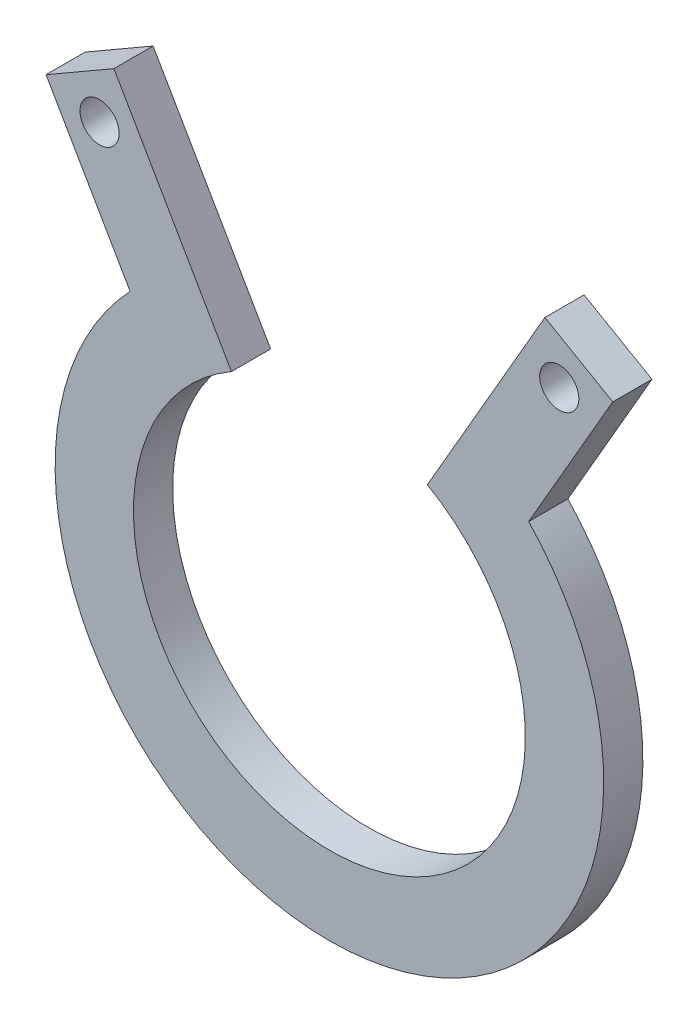
SolidWorks part; units mm, degrees
ref_plane "Front Plane" through (0, 0, 0) normal (0, 0, 1) x (1, 0, 0)
ref_plane "Top Plane" through (0, 0, 0) normal (0, 1, 0) x (1, 0, 0)
ref_plane "Right Plane" through (0, 0, 0) normal (1, 0, 0) x (0, 0, -1)
sketch "Sketch2" plane through (0, 0, 0) normal (0, 0, 1) x (1, 0, 0)
  circle A0 centre (0, 0) radius 19.05
  circle A1 centre (0, 0) radius 22.225
  circle A2 centre (0, 0) radius 15.875
  dimension "D1" = 38.1
  dimension "D2" = 3.175
  dimension "D3" = 3.175
extrude "Boss-Extrude1" add sketch "Sketch2" along normal blind 3.175 contours A1 A0 | A0 A2
sketch "Sketch3" plane through (0, 0, 3.175) normal (0, 0, 1) x (1, 0, 0)
  line L0 (-20.2121, 28.6584) -> (-18.6246, 25.9088) construction
  line L1 (0, 0) -> (-11.1125, 19.2474) construction
  line L2 (0, 0) -> (0, 22.225) construction
  line L3 (-11.1125, 19.2474) -> (-17.4625, 30.2459)
  line L4 (-17.4625, 30.2459) -> (-22.9618, 27.0709)
  line L5 (-22.9618, 27.0709) -> (-16.1485, 15.2701)
  line L6 (-17.4625, 30.2459) -> (-10.6493, 18.4451)
  line L7 (-16.6118, 16.0724) -> (-22.9618, 27.0709)
  line L8 (20.2121, 28.6584) -> (18.6246, 25.9088) construction
  line L9 (16.6118, 16.0724) -> (22.9618, 27.0709)
  line L10 (17.4625, 30.2459) -> (10.6493, 18.4451)
  line L11 (22.9618, 27.0709) -> (16.1485, 15.2701)
  line L12 (17.4625, 30.2459) -> (22.9618, 27.0709)
  line L13 (11.1125, 19.2474) -> (17.4625, 30.2459)
  circle A0 centre (0, 0) radius 22.225 construction
  circle A2 centre (-18.6246, 25.9088) radius 1.5875
  circle A3 centre (18.6246, 25.9088) radius 1.5875
  circle M7 centre (0, 0) radius 22.225
  dimension "D5" = 3.175
  dimension "D1" = 30
  dimension "D2" = 3.175
  dimension "D3" = 12.7
  dimension "D4" = 6.35
extrude "Boss-Extrude2" add sketch "Sketch3" against normal up to surface (3.175 mm away) contours L4 L5 L3 A2 M7 | L12 L10 L11 L9 A3 M7 up to face at (22.225, 0, 0)
ref_plane "Plane4" through (-17.4625, 30.2459, 3.175) normal (0, 0, 1) x (1, 0, 0)
sketch "Sketch5" plane through (0, 0, 3.175) normal (0, 0, 1) x (1, 0, 0)
  line L0 (-11.1125, 19.2474) -> (0, 0)
  line L1 (0, 0) -> (11.1125, 19.2474)
  arc A0 (11.1125, 19.2474) -> (-11.1125, 19.2474) centre (0, 0) ccw construction
  arc A1 (11.1125, 19.2474) -> (-11.1125, 19.2474) centre (0, 0) ccw
extrude "Cut-Extrude1" cut sketch "Sketch5" against normal up to surface (3.175 mm away) up to face at (0, 18.6439, 0)
